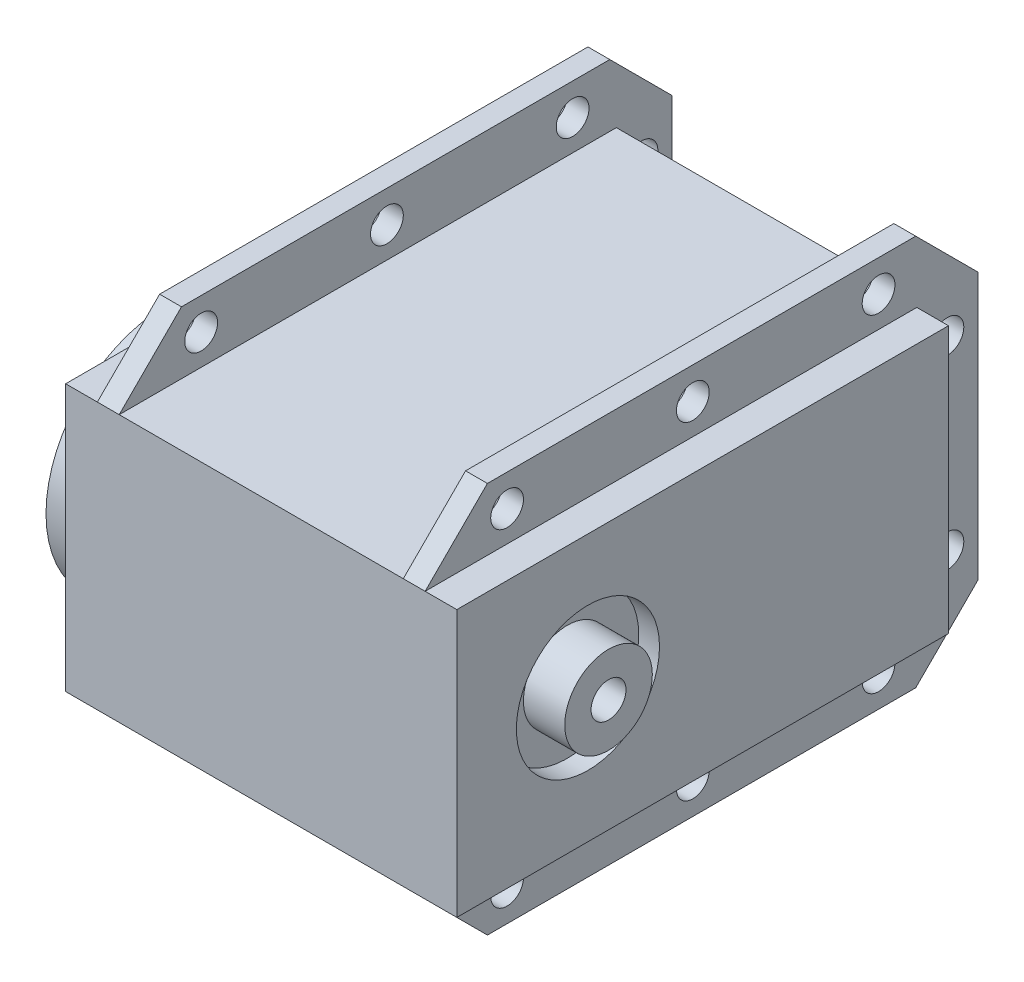
SolidWorks part; units mm, degrees
ref_plane "Front Plane" through (0, 0, 0) normal (0, 0, 1) x (1, 0, 0)
ref_plane "Top Plane" through (0, 0, 0) normal (0, 1, 0) x (1, 0, 0)
ref_plane "Right Plane" through (0, 0, 0) normal (1, 0, 0) x (0, 0, -1)
ref_plane "Plane1" through (181.514, 0, 0) normal (1, 0, 0) x (0, 0, -1)
sketch "Sketch1" plane through (181.514, 0, 0) normal (1, 0, 0) x (0, 0, -1)
  line L0 (-608.2152, 77.3335) -> (-608.2152, 107.4335)
  line L1 (-608.2152, 107.4335) -> (-653.7152, 107.4335)
  line L2 (-653.7152, 107.4335) -> (-653.7152, 77.3335)
  line L3 (-653.7152, 77.3335) -> (-608.2152, 77.3335)
extrude "Boss-Extrude1" add sketch "Sketch1" against normal blind 30
sketch "Sketch2" plane through (0, 0, 608.2152) normal (0, 0, -1) x (-1, 0, 0)
  line L0 (-179.514, 107.4335) -> (-179.514, 101.7335)
  line L1 (-179.514, 101.7335) -> (-151.514, 101.7335)
  line L2 (-151.514, 101.7335) -> (-151.514, 107.4335)
  line L3 (-151.514, 107.4335) -> (-179.514, 107.4335)
extrude "Cut-Extrude1" cut sketch "Sketch2" against normal through all
sketch "Sketch3" plane through (0, 0, 608.2152) normal (0, 0, -1) x (-1, 0, 0)
  line L0 (-181.514, 77.3335) -> (-181.514, 107.4335)
  line L1 (-181.514, 107.4335) -> (-179.514, 107.4335)
  line L2 (-179.514, 107.4335) -> (-179.514, 77.3335)
  line L3 (-179.514, 77.3335) -> (-181.514, 77.3335)
extrude "Boss-Extrude2" add sketch "Sketch3" along normal blind 5.1
sketch "Sketch4" plane through (0, 77.3335, 0) normal (0, -1, 0) x (1, 0, 0)
  line L0 (181.514, 653.7152) -> (181.514, 603.1152)
  line L1 (181.514, 603.1152) -> (179.514, 603.1152)
  line L2 (179.514, 603.1152) -> (179.514, 653.7152)
  line L3 (179.514, 653.7152) -> (181.514, 653.7152)
extrude "Boss-Extrude3" add sketch "Sketch4" along normal blind 5.7
sketch "Sketch5" plane through (0, 77.3335, 0) normal (0, -1, 0) x (1, 0, 0)
  line L0 (151.514, 608.2152) -> (151.514, 653.7152)
  line L1 (151.514, 653.7152) -> (153.514, 653.7152)
  line L2 (153.514, 653.7152) -> (153.514, 608.2152)
  line L3 (153.514, 608.2152) -> (151.514, 608.2152)
extrude "Boss-Extrude4" add sketch "Sketch5" along normal blind 5.7
sketch "Sketch6" plane through (0, 0, 608.2152) normal (0, 0, -1) x (-1, 0, 0)
  line L0 (-151.514, 101.7335) -> (-151.514, 71.6335)
  line L1 (-151.514, 71.6335) -> (-153.514, 71.6335)
  line L2 (-153.514, 71.6335) -> (-153.514, 101.7335)
  line L3 (-153.514, 101.7335) -> (-151.514, 101.7335)
extrude "Boss-Extrude5" add sketch "Sketch6" along normal blind 5.1
sketch "Sketch7" plane through (0, 101.7335, 0) normal (0, 1, 0) x (-1, 0, 0)
  line L0 (-151.514, 653.7152) -> (-151.514, 603.1152)
  line L1 (-151.514, 603.1152) -> (-153.514, 603.1152)
  line L2 (-153.514, 603.1152) -> (-153.514, 653.7152)
  line L3 (-153.514, 653.7152) -> (-151.514, 653.7152)
extrude "Boss-Extrude6" add sketch "Sketch7" along normal blind 5.7
sketch "Sketch8" plane through (151.514, 0, 0) normal (-1, 0, 0) x (0, 0, 1)
  line L0 (608.7152, 77.3335) -> (608.7152, 101.7335)
  line L1 (608.7152, 101.7335) -> (653.7152, 101.7335)
  line L2 (653.7152, 101.7335) -> (653.7152, 77.3335)
  line L3 (653.7152, 77.3335) -> (608.7152, 77.3335)
extrude "Boss-Extrude7" add sketch "Sketch8" along normal blind 2.9
sketch "Sketch9" plane through (181.514, 0, 0) normal (1, 0, 0) x (0, 0, -1)
  line L0 (-608.7152, 77.3335) -> (-653.7152, 77.3335)
  line L1 (-653.7152, 77.3335) -> (-653.7152, 101.7335)
  line L2 (-653.7152, 101.7335) -> (-608.7152, 101.7335)
  line L3 (-608.7152, 101.7335) -> (-608.7152, 77.3335)
extrude "Boss-Extrude8" add sketch "Sketch9" along normal blind 2.9
hole_wizard "M12 Clearance Hole1" positions "Sketch11" profile "Sketch10" hole size "M12" standard "ANSI Metric"
sketch "Sketch11" plane through (184.414, 0, 0) normal (1, 0, 0) x (0, 0, -1)
  point P0 (-641.7152, 89.5335)
sketch "Sketch10" plane through (184.414, 89.5335, 641.7152) normal (0, 1, 0) x (0, 0, -1)
  line L0 (0, 0) -> (0, 1.9)
  line L1 (0, 1.9) -> (6.55, 1.9)
  line L2 (6.55, 1.9) -> (6.55, 0)
  line L5 (6.55, 0) -> (0, 0)
  line L10 (0, 1.9) -> (-6.55, 1.9) construction
  line L11 (0, -6.35) -> (0, 107.95) construction
  dimension "Hole Dia." = 13.1
  dimension "Hole Depth" = 1.9
  dimension "Drill Angle" = 180
ref_plane "Plane2" through (0, 0, 641.7152) normal (0, 0, 1) x (1, 0, 0)
sketch "Sketch12" plane through (0, 0, 641.7152) normal (0, 0, 1) x (1, 0, 0)
  line L0 (182.514, 93.5335) -> (182.514, 89.5255)
  line L1 (182.514, 89.5255) -> (186.2989, 89.5255)
  line L2 (186.2989, 89.5255) -> (186.2989, 93.5335)
  line L3 (186.2989, 93.5335) -> (182.514, 93.5335)
  line L4 (182.514, 89.5255) -> (186.2989, 89.5255) construction
revolve "Revolve1" add sketch "Sketch12" angle 360 about L4
sketch "Sketch13" plane through (0, 0, 641.7152) normal (0, 0, 1) x (1, 0, 0)
  line L0 (142.814, 93.5335) -> (142.814, 89.5335)
  line L1 (142.814, 89.5335) -> (148.614, 89.5335)
  line L2 (148.614, 89.5335) -> (148.614, 93.5335)
  line L3 (148.614, 93.5335) -> (147.814, 93.5335)
  line L4 (147.814, 93.5335) -> (147.814, 100.5335)
  line L5 (147.814, 100.5335) -> (145.814, 100.5335)
  line L6 (145.814, 100.5335) -> (145.814, 93.5335)
  line L7 (145.814, 93.5335) -> (142.814, 93.5335)
  line L8 (142.814, 89.5335) -> (148.614, 89.5335) construction
revolve "Revolve2" add sketch "Sketch13" angle 360 about L8
hole_wizard "Ø3.0 (3) Diameter Hole1" positions "Sketch15" profile "Sketch14" hole size "Ø3.0" standard "ANSI Metric"
sketch "Sketch15" plane through (151.514, 0, 0) normal (-1, 0, 0) x (0, 0, 1)
  point P0 (612.2152, 104.5335)
  point P1 (612.2152, 74.5335)
  point P2 (605.9152, 81.0335)
  point P3 (605.9152, 98.0335)
  point P4 (646.2152, 104.5335)
  point P5 (646.2152, 74.5335)
  point P6 (629.2152, 104.5335)
  point P7 (629.2152, 74.5335)
sketch "Sketch14" plane through (151.514, 104.5335, 612.2152) normal (0, 1, 0) x (0, 0, 1)
  line L0 (0, 0) -> (0, 2)
  line L1 (0, 2) -> (1.5, 2)
  line L2 (1.5, 2) -> (1.5, 0)
  line L5 (1.5, 0) -> (0, 0)
  line L11 (0, -6.35) -> (0, 107.95) construction
  dimension "Thru Hole Dia." = 3
  dimension "Thru Hole Depth" = 2
hole_wizard "Ø3.0 (3) Diameter Hole2" positions "Sketch17" profile "Sketch16" hole size "Ø3.0" standard "ANSI Metric"
sketch "Sketch17" plane through (181.514, 0, 0) normal (1, 0, 0) x (0, 0, -1)
  point P0 (-605.9152, 81.0335)
sketch "Sketch16" plane through (181.514, 81.0335, 605.9152) normal (0, 1, 0) x (0, 0, -1)
  line L0 (0, 0) -> (0, 38.7)
  line L1 (0, 38.7) -> (1.5, 38.7)
  line L2 (1.5, 38.7) -> (1.5, 0)
  line L5 (1.5, 0) -> (0, 0)
  line L11 (0, -6.35) -> (0, 107.95) construction
  dimension "Thru Hole Dia." = 3
  dimension "Thru Hole Depth" = 38.7
hole_wizard "Ø3.0 (3) Diameter Hole3" positions "Sketch19" profile "Sketch18" hole size "Ø3.0" standard "ANSI Metric"
sketch "Sketch19" plane through (179.514, 0, 0) normal (-1, 0, 0) x (0, 0, 1)
  point P0 (612.2152, 104.5335)
  point P1 (612.2152, 74.5335)
  point P2 (605.9152, 98.0335)
  point P3 (629.2152, 74.5335)
  point P4 (629.2152, 104.5335)
  point P5 (646.2152, 74.5335)
  point P6 (646.2152, 104.5335)
sketch "Sketch18" plane through (179.514, 104.5335, 612.2152) normal (0, 1, 0) x (0, 0, 1)
  line L0 (0, 0) -> (0, 6.7849)
  line L1 (0, 6.7849) -> (1.5, 6.7849)
  line L2 (1.5, 6.7849) -> (1.5, 0)
  line L5 (1.5, 0) -> (0, 0)
  line L11 (0, -6.35) -> (0, 107.95) construction
  dimension "Thru Hole Dia." = 3
  dimension "Thru Hole Depth" = 6.7849
hole_wizard "Ø2.0 (2) Diameter Hole1" positions "Sketch21" profile "Sketch20" hole size "Ø2.0" standard "ANSI Metric"
sketch "Sketch21" plane through (145.814, 0, 0) normal (-1, 0, 0) x (0, 0, 1)
  point P0 (641.7152, 98.0335)
  point P1 (641.7152, 81.0335)
  point P2 (633.2152, 89.5335)
  point P3 (650.2152, 89.5335)
sketch "Sketch20" plane through (145.814, 98.0335, 641.7152) normal (0, 1, 0) x (0, 0, 1)
  line L0 (0, 0) -> (0, 2)
  line L1 (0, 2) -> (1, 2)
  line L2 (1, 2) -> (1, 0)
  line L5 (1, 0) -> (0, 0)
  line L11 (0, -6.35) -> (0, 107.95) construction
  dimension "Thru Hole Dia." = 2
  dimension "Thru Hole Depth" = 2
hole_wizard "M2x0.4 Tapped Hole1" positions "Sketch23" profile "Sketch22" tap size "M2x0.4" standard "ANSI Metric"
sketch "Sketch23" plane through (142.814, 0, 0) normal (-1, 0, 0) x (0, 0, 1)
  point P0 (641.7152, 89.5335)
sketch "Sketch22" plane through (142.814, 89.5335, 641.7152) normal (0, 1, 0) x (0, 0, 1)
  line L0 (0, 0) -> (0, 1.8)
  line L1 (0, 1.8) -> (2.5, 1.8)
  line L2 (2.5, 1.8) -> (2.5, 1)
  line L3 (2.5, 1) -> (1.25, 1)
  line L4 (1.25, 1) -> (1.25, 0)
  line L5 (1.25, 0) -> (0, 0)
  line L10 (0, 1.8) -> (-2.5, 1.8) construction
  line L11 (0, -6.35) -> (0, 107.95) construction
  dimension "Tap Drill Dia." = 5
  dimension "Tap Drill Depth" = 1.8
  dimension "Thread Major Dia." = 2.5
  dimension "Thread Depth" = 1
  dimension "Drill Angle" = 180
chamfer "Chamfer1" distance 5.7 angle 45 8 edges at (152.514, 107.4335, 603.1152) (152.514, 71.6335, 653.7152) (152.514, 71.6335, 603.1152) (180.514, 71.6335, 603.1152) (152.514, 107.4335, 653.7152) (180.514, 107.4335, 653.7152) (180.514, 107.4335, 603.1152) (180.514, 71.6335, 653.7152)
ref_plane "Plane3" through (187.514, 0, 0) normal (1, 0, 0) x (0, 0, -1)
sketch "Sketch24" plane through (186.2989, 0, 0) normal (1, 0, 0) x (0, 0, -1)
  circle A0 centre (-641.7152, 89.5255) radius 1.6
  dimension "D1" = 3.2
extrude "Cut-Extrude2" cut sketch "Sketch24" against normal blind 10
